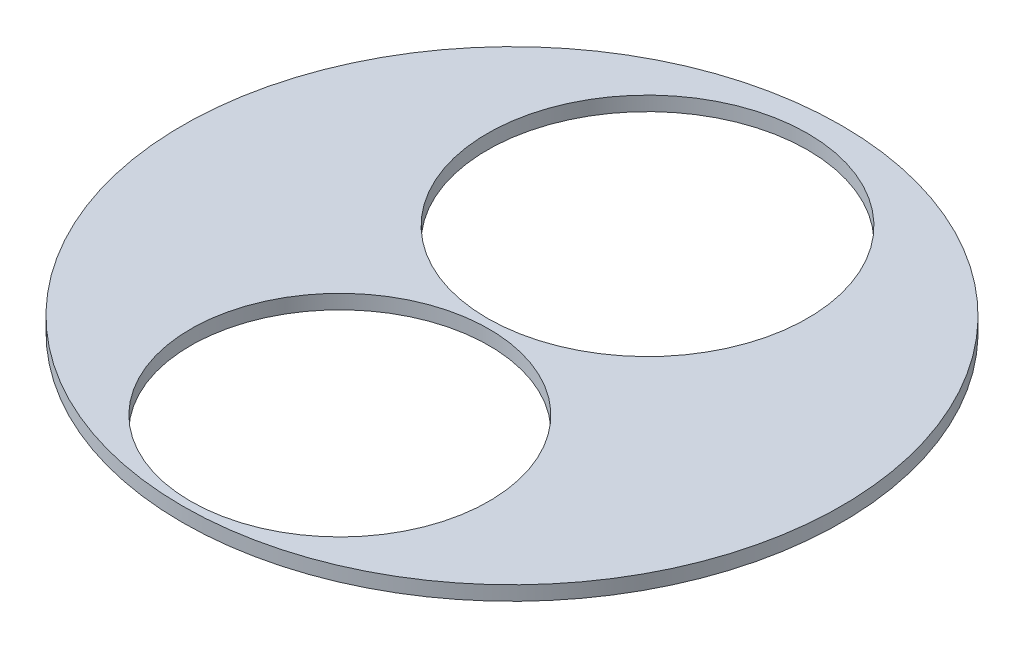
SolidWorks part; units mm, degrees
ref_plane "Front Plane" through (0, 0, 0) normal (0, 0, 1) x (1, 0, 0)
ref_plane "Top Plane" through (0, 0, 0) normal (0, 1, 0) x (1, 0, 0)
ref_plane "Right Plane" through (0, 0, 0) normal (1, 0, 0) x (0, 0, -1)
sketch "Sketch1" plane through (0, 0, 0) normal (0, 1, 0) x (1, 0, 0)
  circle A0 centre (0, 0) radius 1149.985
  circle A1 centre (-35.2158, 508.0712) radius 558.8
  circle A2 centre (0, -600.7589) radius 520.7
  point P5 (0, -600.7589)
  point P6 (-26.9219, 485.8986)
  point P7 (-35.2158, 508.0712)
  dimension "D1" = 2299.97
extrude "Boss-Extrude1" add sketch "Sketch1" along normal blind 50
